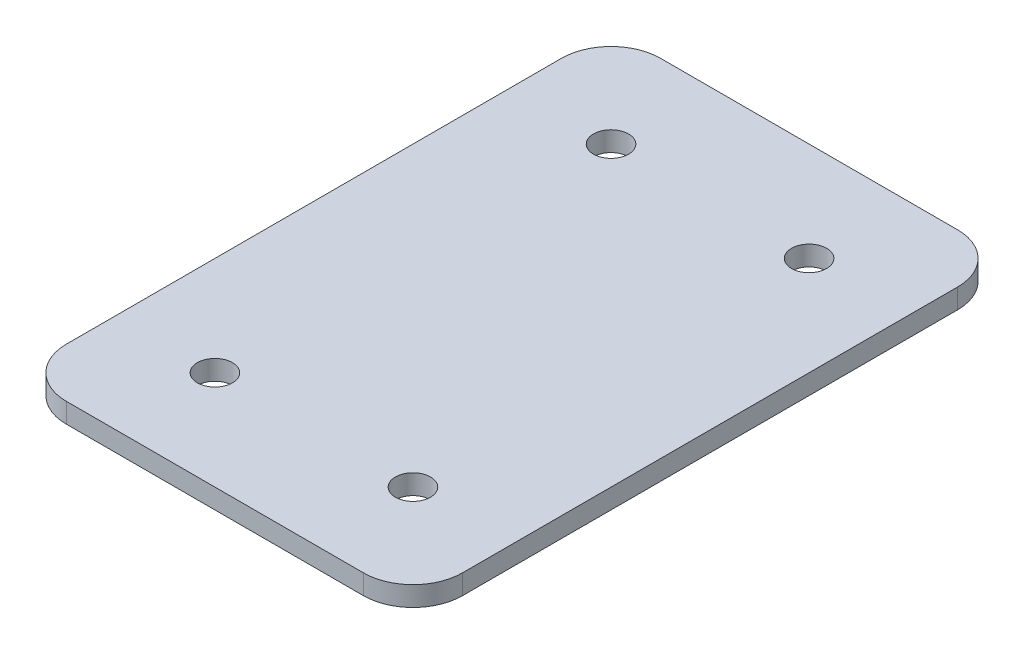
SolidWorks part; units mm, degrees
ref_plane "Front Plane" through (0, 0, 0) normal (0, 0, 1) x (1, 0, 0)
ref_plane "Top Plane" through (0, 0, 0) normal (0, 1, 0) x (1, 0, 0)
ref_plane "Right Plane" through (0, 0, 0) normal (1, 0, 0) x (0, 0, -1)
sketch "Sketch1" plane through (0, 0, 0) normal (0, 1, 0) x (1, 0, 0)
  line L0 (25.4, 76.2) -> (25.4, 0)
  line L1 (6.35, 0) -> (44.45, 0)
  line L2 (0, 6.35) -> (0, 69.85)
  line L3 (6.35, 76.2) -> (44.45, 76.2)
  line L4 (50.8, 6.35) -> (50.8, 69.85)
  line L5 (50.8, 38.1) -> (0, 38.1) construction
  circle A0 centre (38.1, 12.7) radius 2.25
  circle A2 centre (12.7, 12.7) radius 2.25
  circle A3 centre (38.1, 63.5) radius 2.25
  circle A4 centre (12.7, 63.5) radius 2.25
  arc A5 (6.35, 0) -> (0, 6.35) centre (6.35, 6.35) cw
  arc A6 (44.45, 0) -> (50.8, 6.35) centre (44.45, 6.35) ccw
  arc A7 (44.45, 76.2) -> (50.8, 69.85) centre (44.45, 69.85) cw
  arc A8 (0, 69.85) -> (6.35, 76.2) centre (6.35, 69.85) cw
  point P19 (0, 0)
  point P22 (50.8, 0)
  point P27 (0, 76.2)
  dimension "D5" = 4.5
  dimension "D6" = 6.35
  dimension "D1" = 76.2
  dimension "D2" = 50.8
  dimension "D3" = 12.7
  dimension "D4" = 12.7
extrude "Boss-Extrude1" add sketch "Sketch1" along normal blind 2.54 contours L4 L5 L0 L1 A6 A0 | L5 L4 A7 L3 L0 A3 | L5 L0 L3 A8 L2 A4 | L0 L5 L2 A5 L1 A2
